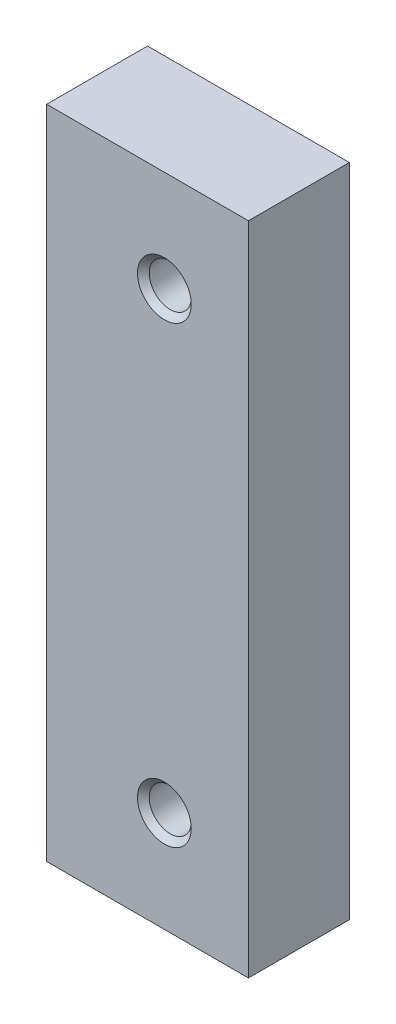
SolidWorks part; units mm, degrees
ref_plane "Спереди" through (0, 0, 0) normal (0, 0, 1) x (1, 0, 0)
ref_plane "Сверху" through (0, 0, 0) normal (0, 1, 0) x (1, 0, 0)
ref_plane "Справа" through (0, 0, 0) normal (1, 0, 0) x (0, 0, -1)
sketch "Эскиз1" plane through (0, 0, 0) normal (0, 1, 0) x (1, 0, 0)
  line L1 (0, 0) -> (12, 0)
  line L2 (0, 0) -> (0, 6)
  line L3 (0, 6) -> (12, 6)
  line L4 (12, 0) -> (12, 6)
  dimension "D1" = 6
  dimension "D2" = 12
extrude "Бобышка-Вытянуть1" add sketch "Эскиз1" along normal blind 39
hole_wizard "Отверстие обработанное метчиком M31" positions "Эскиз3" profile "Эскиз2" tap size "M3" standard "DIN" end condition through all
sketch "Эскиз3" plane through (0, 0, 0) normal (0, 0, 1) x (1, 0, 0)
  line L0 (12, 39) -> (12, 0) construction
  line L2 (0, 0) -> (12, 0) construction
  point P0 (7, 6)
  point P1 (7, 33)
  dimension "D1" = 5
  dimension "D2" = 27
  dimension "D3" = 6
sketch "Эскиз2" plane through (7, 6, 0) normal (1, 0, 0) x (0, -1, 0)
  line L0 (0, 0) -> (0, 6)
  line L1 (0, 6) -> (1.6, 6)
  line L2 (1.25, 5.65) -> (1.25, 0.35)
  line L3 (1.25, 0.35) -> (1.6, 0)
  line L5 (1.6, 0) -> (0, 0)
  line L6 (-1.25, 0.35) -> (-1.6, 0) construction
  line L7 (1.6, 6) -> (1.25, 5.65)
  line L8 (-1.6, 6) -> (-1.25, 5.65) construction
  line L11 (0, -6.35) -> (0, 107.95) construction
  dimension "Диаметр проходного сверла" = 2.5
  dimension "Глубина проходного сверла" = 6
  dimension "Диаметр передней зенковки" = 3.2
  dimension "Угол передней зенковки" = 90
  dimension "Диаметр задней зенковки" = 3.2
  dimension "Угол задней зенковки" = 90
cosmetic thread "Отверстие резьбы1" parameters "D2"=3
cosmetic thread "Отверстие резьбы2" parameters "D2"=3
